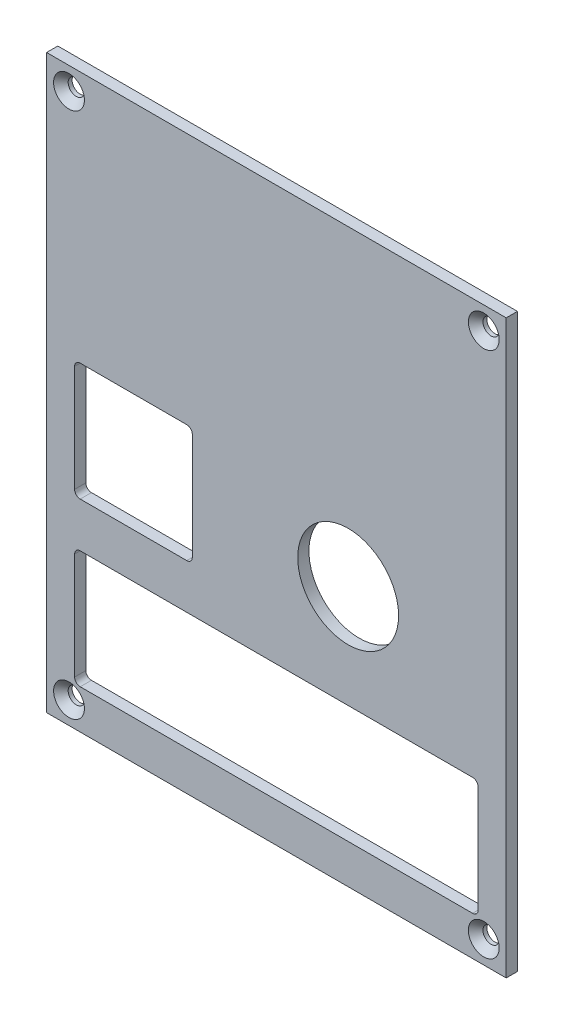
SolidWorks part; units mm, degrees
ref_plane "Front Plane" through (0, 0, 0) normal (0, 0, 1) x (1, 0, 0)
ref_plane "Top Plane" through (0, 0, 0) normal (0, 1, 0) x (1, 0, 0)
ref_plane "Right Plane" through (0, 0, 0) normal (1, 0, 0) x (0, 0, -1)
sketch "Sketch1" plane through (0, 0, 0) normal (0, 0, 1) x (1, 0, 0)
  line L1 (-49.4982, 55.7269) -> (32.5018, 55.7269)
  line L2 (-49.4982, 55.7269) -> (-49.4982, -46.2731)
  line L3 (-49.4982, -46.2731) -> (32.5018, -46.2731)
  line L4 (32.5018, 55.7269) -> (32.5018, -46.2731)
  dimension "D1" = 82
  dimension "D2" = 102
extrude "Boss-Extrude1" add sketch "Sketch1" along normal blind 2
sketch "Sketch2" plane through (0, 0, 2) normal (0, 0, 1) x (1, 0, 0)
  line L3 (-43.4982, -18.2731) -> (26.5018, -18.2731)
  line L4 (-44.4982, -19.2731) -> (-44.4982, -38.2731)
  line L5 (-43.4982, -39.2731) -> (26.5018, -39.2731)
  line L6 (27.5018, -19.2731) -> (27.5018, -38.2731)
  line L7 (-49.4982, 55.7269) -> (-49.4982, -46.2731) construction
  line L8 (-49.4982, -46.2731) -> (32.5018, -46.2731) construction
  line L15 (-43.4982, 10.7269) -> (-24.4982, 10.7269)
  line L16 (-44.4982, 9.7269) -> (-44.4982, -9.2731)
  line L17 (-43.4982, -10.2731) -> (-24.4982, -10.2731)
  line L18 (-23.4982, 9.7269) -> (-23.4982, -9.2731)
  arc A2 (26.5018, -18.2731) -> (27.5018, -19.2731) centre (26.5018, -19.2731) cw
  arc A3 (-44.4982, -38.2731) -> (-43.4982, -39.2731) centre (-43.4982, -38.2731) ccw
  arc A4 (26.5018, -39.2731) -> (27.5018, -38.2731) centre (26.5018, -38.2731) ccw
  arc A5 (-43.4982, -18.2731) -> (-44.4982, -19.2731) centre (-43.4982, -19.2731) ccw
  arc A6 (-44.4982, -9.2731) -> (-43.4982, -10.2731) centre (-43.4982, -9.2731) ccw
  arc A7 (-24.4982, -10.2731) -> (-23.4982, -9.2731) centre (-24.4982, -9.2731) ccw
  arc A8 (-24.4982, 10.7269) -> (-23.4982, 9.7269) centre (-24.4982, 9.7269) cw
  arc A9 (-43.4982, 10.7269) -> (-44.4982, 9.7269) centre (-43.4982, 9.7269) ccw
  circle A11 centre (4.3018, 0.1122) radius 9
  point P11 (27.5018, -18.2731)
  point P14 (-44.4982, -39.2731)
  point P18 (27.5018, -39.2731)
  point P27 (-23.4982, -10.2731)
  point P30 (-23.4982, 10.7269)
  point P33 (-44.4982, 10.7269)
  dimension "D1" = 72
  dimension "D5" = 1
  dimension "D6" = 1
  dimension "D11" = 1
  dimension "D12" = 18
  dimension "D2" = 5
  dimension "D3" = 21
  dimension "D4" = 7
  dimension "D7" = 21
  dimension "D8" = 21
  dimension "D9" = 5
  dimension "D10" = 8
extrude "Cut-Extrude2" cut sketch "Sketch2" against normal blind 2
sketch "Sketch16" plane through (0, 0, 2) normal (0, 0, 1) x (1, 0, 0)
  line L0 (-49.4982, 55.7269) -> (-49.4982, -46.2731) construction
  line L1 (-49.4982, -46.2731) -> (32.5018, -46.2731) construction
  line L2 (32.5018, 55.7269) -> (-49.4982, 55.7269) construction
  line L3 (32.5018, -46.2731) -> (32.5018, 55.7269) construction
  point P0 (-45.4982, -42.2731)
  point P1 (28.5018, -42.2731)
  point P2 (28.5018, 51.7269)
  point P3 (-45.4982, 51.7269)
  dimension "D1" = 4
  dimension "D2" = 4
  dimension "D3" = 4
  dimension "D4" = 4
  dimension "D5" = 4
  dimension "D6" = 4
  dimension "D7" = 4
  dimension "D8" = 4
hole_wizard "CSK for M2.5 Countersunk Flat Head Screw2" positions "Sketch17" profile "Sketch18" countersink size "M2.5" standard "ISO" end condition through all
sketch "Sketch17" plane through (0, 0, 2) normal (0, 0, 1) x (1, 0, 0)
  point P0 (-45.4982, 51.7269)
  point P3 (-45.4982, -42.2731)
  point P6 (28.5018, -42.2731)
  point P9 (28.5018, 51.7269)
sketch "Sketch18" plane through (-45.4982, 51.7269, 2) normal (1, 0, 0) x (0, -1, 0)
  line L0 (0, 0) -> (0, 2)
  line L1 (0, 2) -> (1.45, 2)
  line L2 (1.45, 2) -> (1.45, 1.3)
  line L3 (1.45, 1.3) -> (2.75, 0)
  line L5 (2.75, 0) -> (0, 0)
  line L6 (-1.45, 1.3) -> (-2.75, 0) construction
  line L11 (0, -6.35) -> (0, 107.95) construction
  dimension "Thru Hole Dia." = 2.9
  dimension "Thru Hole Depth" = 2
  dimension "Near C'Sink Dia." = 5.5
  dimension "Near C'Sink Angle" = 90
